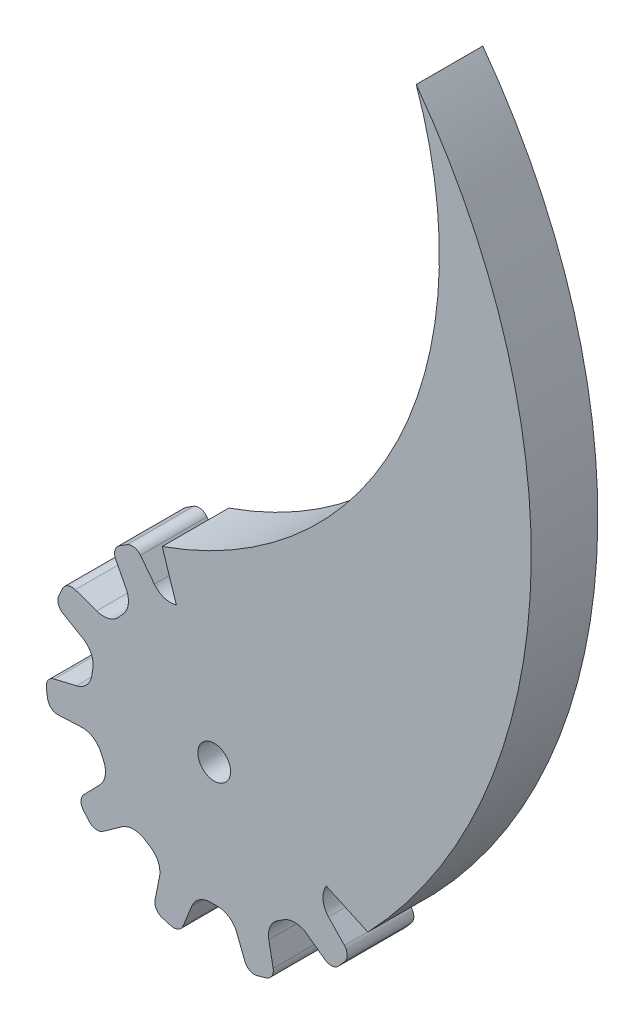
SolidWorks part; units mm, degrees
ref_plane "Plano frontal" through (0, 0, 0) normal (0, 0, 1) x (1, 0, 0)
ref_plane "Plano superior" through (0, 0, 0) normal (0, 1, 0) x (1, 0, 0)
ref_plane "Plano direito" through (0, 0, 0) normal (1, 0, 0) x (0, 0, -1)
sketch "Esboço1" plane through (0, 0, 0) normal (0, 0, 1) x (1, 0, 0)
  line L0 (7.2373, 13.8826) -> (5.841, 12.1155)
  line L1 (9.6438, 12.3222) -> (8.6103, 10.3584)
  line L2 (13.5939, 7.766) -> (11.4639, 7.0343)
  line L3 (14.7748, 5.1522) -> (12.8436, 4.059)
  line L4 (15.6346, -0.8162) -> (13.4471, -0.2802)
  line L5 (15.2149, -3.6535) -> (12.9992, -3.5291)
  line L6 (12.7114, -9.1393) -> (11.1609, -7.5058)
  line L7 (10.8243, -11.2993) -> (9.0276, -9.9968)
  line L8 (5.7524, -14.5608) -> (5.3312, -12.3483)
  line L9 (2.9971, -15.3576) -> (2.1899, -13.2906)
  line L10 (-1.4171, 15.5916) -> (-1.6364, 13.3501)
  line L11 (1.451, 15.5799) -> (1.6432, 13.3691)
  line L12 (-3.0329, -15.3593) -> (-2.1911, -13.2703)
  line L13 (-5.7816, -14.54) -> (-5.3432, -12.3647)
  line L14 (-10.8553, -11.2813) -> (-9.0177, -9.9791)
  line L15 (-12.7248, -9.1061) -> (-11.1798, -7.5131)
  line L16 (-15.2312, -3.6216) -> (-12.9813, -3.5196)
  line L17 (-15.6279, -0.781) -> (-13.4669, -0.2761)
  line L18 (-14.7713, 5.1879) -> (-12.8234, 4.0573)
  line L19 (-13.5692, 7.792) -> (-11.4784, 7.0485)
  line L20 (-9.6216, 12.3503) -> (-8.5942, 10.3461)
  line L21 (-7.2025, 13.8912) -> (-5.8455, 12.1352)
  arc A0 (-3.1096, 11.6128) -> (-3.655, 11.4529) centre (0, 0) ccw
  circle A1 centre (0, 0) radius 1.6
  arc A2 (0.4841, 16.4929) -> (-0.4491, 16.4939) centre (0, 0) ccw
  arc A3 (1.451, 15.5799) -> (0.4841, 16.4929) centre (0.4548, 15.4933) ccw
  arc A4 (-1.4171, 15.5916) -> (-0.4491, 16.4939) centre (-0.4219, 15.4943) cw
  arc A5 (9.324, 13.613) -> (8.5395, 14.1183) centre (0, 0) ccw
  arc A6 (9.6438, 12.3222) -> (9.324, 13.613) centre (8.7589, 12.7879) ccw
  arc A7 (7.2373, 13.8826) -> (8.5395, 14.1183) centre (8.0219, 13.2627) cw
  arc A8 (15.2036, 6.411) -> (14.8168, 7.2603) centre (0, 0) ccw
  arc A9 (14.7748, 5.1522) -> (15.2036, 6.411) centre (14.2821, 6.0225) ccw
  arc A10 (13.5939, 7.766) -> (14.8168, 7.2603) centre (13.9188, 6.8203) cw
  arc A11 (16.2561, -2.8264) -> (16.3899, -1.9028) centre (0, 0) ccw
  arc A12 (15.2149, -3.6535) -> (16.2561, -2.8264) centre (15.2709, -2.6551) ccw
  arc A13 (15.6346, -0.8162) -> (16.3899, -1.9028) centre (15.3966, -1.7875) cw
  arc A14 (12.1475, -11.1664) -> (12.7593, -10.4618) centre (0, 0) ccw
  arc A15 (10.8243, -11.2993) -> (12.1475, -11.1664) centre (11.4113, -10.4897) ccw
  arc A16 (12.7114, -9.1393) -> (12.7593, -10.4618) centre (11.986, -9.8277) cw
  arc A17 (4.1821, -15.9612) -> (5.0778, -15.6992) centre (0, 0) ccw
  arc A18 (2.9971, -15.3576) -> (4.1821, -15.9612) centre (3.9286, -14.9939) ccw
  arc A19 (5.7524, -14.5608) -> (5.0778, -15.6992) centre (4.77, -14.7478) cw
  arc A20 (-5.1111, -15.6884) -> (-4.216, -15.9523) centre (0, 0) ccw
  arc A21 (-5.7816, -14.54) -> (-5.1111, -15.6884) centre (-4.8013, -14.7376) ccw
  arc A22 (-3.0329, -15.3593) -> (-4.216, -15.9523) centre (-3.9605, -14.9855) cw
  arc A23 (-12.7815, -10.4347) -> (-12.1712, -11.1406) centre (0, 0) ccw
  arc A24 (-12.7248, -9.1061) -> (-12.7815, -10.4347) centre (-12.0069, -9.8023) ccw
  arc A25 (-10.8553, -11.2813) -> (-12.1712, -11.1406) centre (-11.4335, -10.4654) cw
  arc A26 (-16.3939, -1.868) -> (-16.2621, -2.7918) centre (0, 0) ccw
  arc A27 (-15.6279, -0.781) -> (-16.3939, -1.868) centre (-15.4003, -1.7548) ccw
  arc A28 (-15.2312, -3.6216) -> (-16.2621, -2.7918) centre (-15.2765, -2.6226) cw
  arc A29 (-14.8014, 7.2918) -> (-15.1899, 6.4433) centre (0, 0) ccw
  arc A30 (-13.5692, 7.792) -> (-14.8014, 7.2918) centre (-13.9043, 6.8498) ccw
  arc A31 (-14.7713, 5.1879) -> (-15.1899, 6.4433) centre (-14.2693, 6.0528) cw
  arc A32 (-8.5095, 14.1364) -> (-9.2951, 13.6327) centre (0, 0) ccw
  arc A33 (-7.2025, 13.8912) -> (-8.5095, 14.1364) centre (-7.9937, 13.2797) ccw
  arc A34 (-9.6216, 12.3503) -> (-9.2951, 13.6327) centre (-8.7317, 12.8065) cw
  arc A35 (-8.8943, 8.0882) -> (-9.2666, 7.6587) centre (0, 0) ccw
  arc A36 (-11.8551, 1.9956) -> (-11.9362, 1.433) centre (0, 0) ccw
  arc A37 (-11.0521, -4.7306) -> (-10.8161, -5.2477) centre (0, 0) ccw
  arc A38 (-6.7401, -9.9548) -> (-6.262, -10.2623) centre (0, 0) ccw
  arc A39 (-0.2881, -12.0185) -> (0.2803, -12.0187) centre (0, 0) ccw
  arc A40 (6.2553, -10.2664) -> (6.7335, -9.9592) centre (0, 0) ccw
  arc A41 (10.8127, -5.2547) -> (11.049, -4.7378) centre (0, 0) ccw
  arc A42 (11.9372, 1.4252) -> (11.8564, 1.9878) centre (0, 0) ccw
  arc A43 (9.2716, 7.6527) -> (8.8996, 8.0824) centre (0, 0) ccw
  arc A44 (3.6624, 11.4505) -> (3.1171, 11.6108) centre (0, 0) ccw
  arc A45 (-12.8234, 4.0573) -> (-11.8551, 1.9956) centre (-13.8274, 2.3276) cw
  arc A46 (-13.4669, -0.2761) -> (-11.9362, 1.433) centre (-13.922, 1.6714) ccw
  arc A47 (-12.9813, -3.5196) -> (-11.0521, -4.7306) centre (-12.8907, -5.5176) cw
  arc A48 (-11.1798, -7.5131) -> (-10.8161, -5.2477) centre (-12.6155, -6.1207) ccw
  arc A49 (-9.0177, -9.9791) -> (-6.7401, -9.9548) centre (-7.8614, -11.6109) cw
  arc A50 (-5.3432, -12.3647) -> (-6.262, -10.2623) centre (-7.3038, -11.9695) ccw
  arc A51 (-2.1911, -13.2703) -> (-0.2881, -12.0185) centre (-0.336, -14.0179) cw
  arc A52 (2.1899, -13.2906) -> (0.2803, -12.0187) centre (0.3269, -14.0181) ccw
  arc A53 (5.3312, -12.3483) -> (6.2553, -10.2664) centre (7.2959, -11.9743) cw
  arc A54 (9.0276, -9.9968) -> (6.7335, -9.9592) centre (7.8538, -11.6161) ccw
  arc A55 (11.1609, -7.5058) -> (10.8127, -5.2547) centre (12.6115, -6.1289) cw
  arc A56 (12.9992, -3.5291) -> (11.049, -4.7378) centre (12.8871, -5.526) ccw
  arc A57 (13.4471, -0.2802) -> (11.9372, 1.4252) centre (13.923, 1.6623) cw
  arc A58 (12.8436, 4.059) -> (11.8564, 1.9878) centre (13.8289, 2.3185) ccw
  arc A59 (11.4639, 7.0343) -> (9.2716, 7.6527) centre (10.8141, 8.9258) cw
  arc A60 (8.6103, 10.3584) -> (8.8996, 8.0824) centre (10.3801, 9.427) ccw
  arc A61 (5.841, 12.1155) -> (3.6624, 11.4505) centre (4.2717, 13.3554) cw
  arc A62 (3.1171, 11.6108) -> (1.6432, 13.3691) centre (3.6357, 13.5424) cw
  arc A63 (-3.1096, 11.6128) -> (-1.6364, 13.3501) centre (-3.6269, 13.5448) ccw
  arc A64 (-5.8455, 12.1352) -> (-3.655, 11.4529) centre (-4.263, 13.3582) ccw
  arc A65 (-8.5942, 10.3461) -> (-8.8943, 8.0882) centre (-10.374, 9.4337) cw
  arc A66 (-11.4784, 7.0485) -> (-9.2666, 7.6587) centre (-10.8083, 8.9329) ccw
  point P94 (0, 0)
  dimension "D1" = 1
  dimension "D2" = 11
  dimension "D3" = 2
extrude "Ressalto-extrusão1" add sketch "Esboço1" along normal blind 6.5
sketch "Esboço6" plane through (0, 0, 6.5) normal (0, 0, 1) x (1, 0, 0)
  line L0 (0, 0) -> (19.7211, 67.1646) construction
  line L1 (-5.0778, 15.6992) -> (-3.3852, 10.4662)
  line L2 (15.0017, -6.8702) -> (10.0011, -4.5802)
  arc A0 (19.7211, 67.1646) -> (-5.0778, 15.6992) centre (-18.411, 53.8314) cw
  arc A2 (19.7211, 67.1646) -> (15.0017, -6.8702) centre (-26.7542, 32.9594) cw
  circle A4 centre (0, 0) radius 11
  dimension "D1" = 70
extrude "Ressalto-extrusão2" add sketch "Esboço6" against normal blind 6.5 contours L0 A4 L2 A2 A0 | A4 L0 A0 L1
